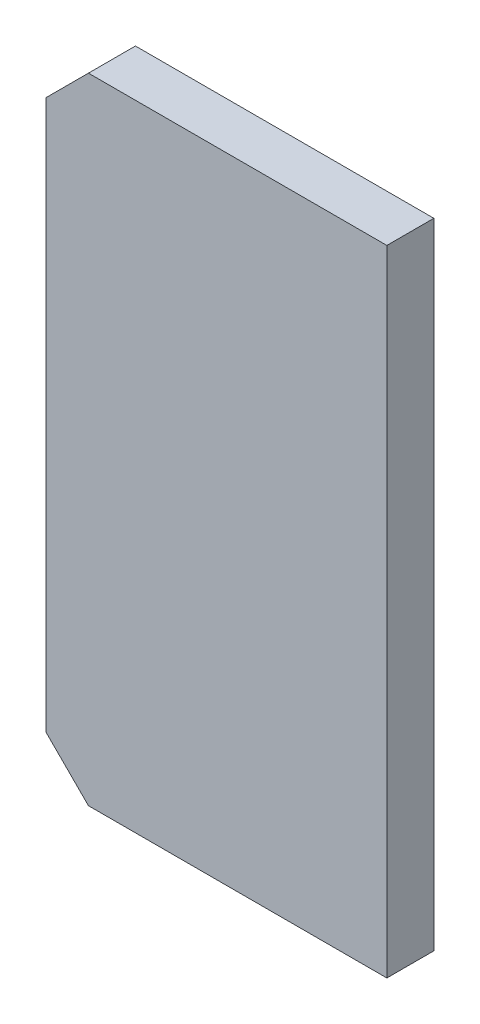
SolidWorks part; units mm, degrees
ref_plane "Спереди" through (0, 0, 0) normal (0, 0, 1) x (1, 0, 0)
ref_plane "Сверху" through (0, 0, 0) normal (0, 1, 0) x (1, 0, 0)
ref_plane "Справа" through (0, 0, 0) normal (1, 0, 0) x (0, 0, -1)
sketch "Эскиз1" plane through (0, 0, 0) normal (0, 0, 1) x (1, 0, 0)
  line L0 (0, 135) -> (-127, 135)
  line L1 (-145, 117) -> (-145, -117)
  line L2 (-127, -135) -> (0, -135)
  line L3 (0, -135) -> (0, 135)
  line L4 (-127, 135) -> (-145, 117)
  line L5 (-127, -135) -> (-145, -117)
extrude "Бобышка-Вытянуть1" add sketch "Эскиз1" along normal blind 20
